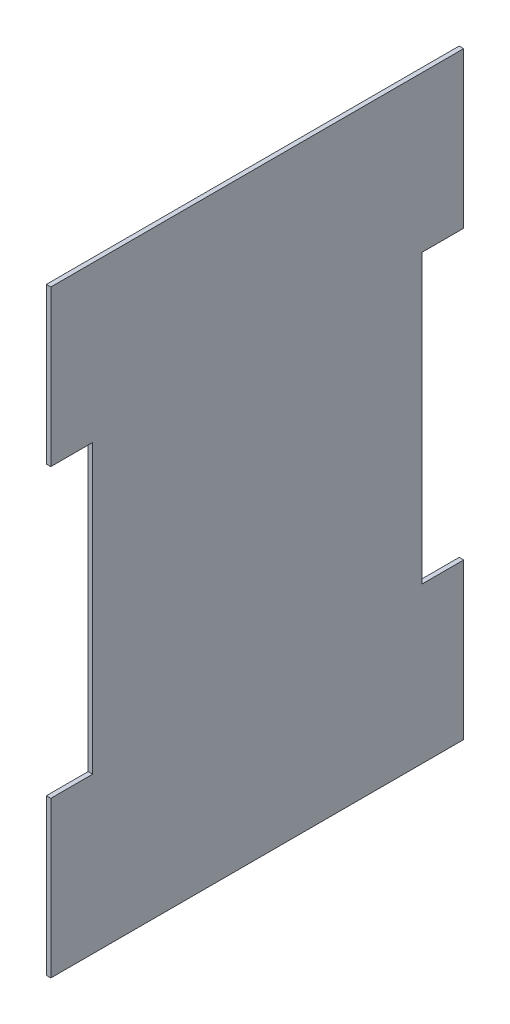
SolidWorks part; units mm, degrees
ref_plane "Front Plane" through (0, 0, 0) normal (0, 0, 1) x (1, 0, 0)
ref_plane "Top Plane" through (0, 0, 0) normal (0, 1, 0) x (1, 0, 0)
ref_plane "Right Plane" through (0, 0, 0) normal (1, 0, 0) x (0, 0, -1)
sketch "Sketch1" plane through (0, 0, 0) normal (1, 0, 0) x (0, 0, -1)
  line L1 (-261.6923, 190.5385) -> (14.3077, 190.5385)
  line L2 (-261.6923, 190.5385) -> (-261.6923, -209.4615)
  line L3 (-261.6923, -209.4615) -> (14.3077, -209.4615)
  line L4 (14.3077, 190.5385) -> (14.3077, -209.4615)
  dimension "D1" = 400
  dimension "D2" = 276
extrude "Boss-Extrude1" add sketch "Sketch1" along normal blind 3
sketch "Sketch2" plane through (0, 0, 0) normal (1, 0, 0) x (0, 0, -1)
  line L0 (-261.6923, -9.4615) -> (14.3077, -9.4615) construction
  line L1 (-261.6923, 190.5385) -> (-261.6923, -209.4615) construction
  line L2 (14.3077, -209.4615) -> (14.3077, 190.5385) construction
  line L3 (-123.6923, 190.5385) -> (-123.6923, -209.4615) construction
  line L4 (14.3077, 190.5385) -> (-261.6923, 190.5385) construction
  line L5 (-261.6923, -209.4615) -> (14.3077, -209.4615) construction
  line L22 (14.3077, -105.4615) -> (-13.6923, -105.4615)
  line L23 (-261.6923, 86.5385) -> (-233.6923, 86.5385)
  line L24 (-261.6923, 86.5385) -> (-261.6923, -105.4615)
  line L25 (-261.6923, -105.4615) -> (-233.6923, -105.4615)
  line L26 (-233.6923, 86.5385) -> (-233.6923, -105.4615)
  line L27 (14.3077, 86.5385) -> (14.3077, -105.4615)
  line L28 (14.3077, 86.5385) -> (-13.6923, 86.5385)
  line L29 (-13.6923, 86.5385) -> (-13.6923, -105.4615)
  dimension "D3" = 192
  dimension "D4" = 96
  dimension "D5" = 28
extrude "Cut-Extrude1" cut sketch "Sketch2" along normal blind 25
